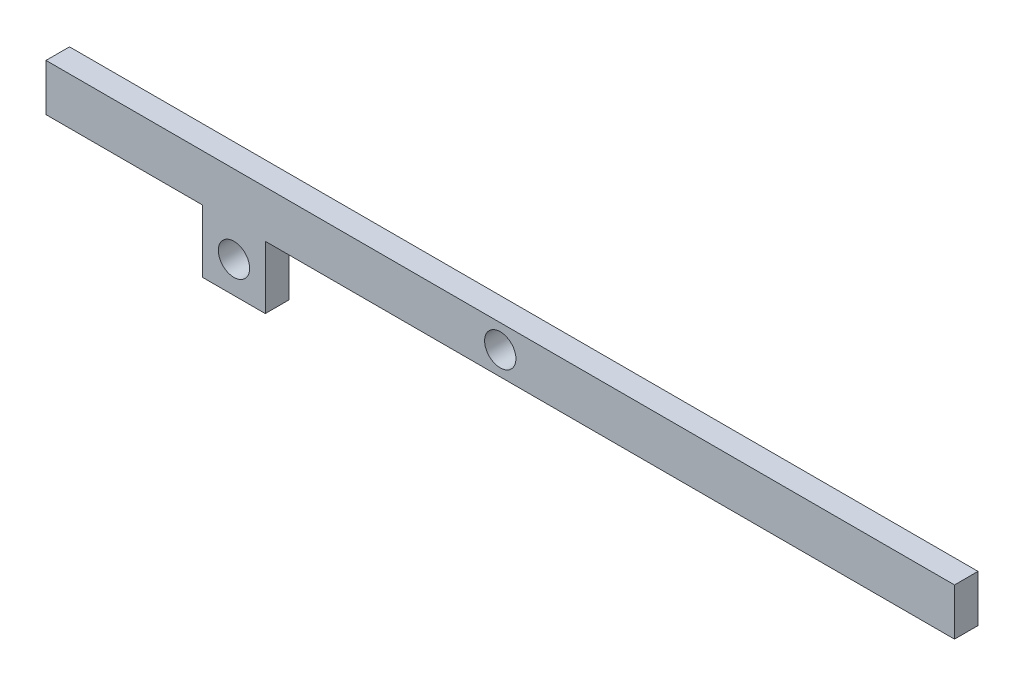
SolidWorks part; units mm, degrees
ref_plane "Front Plane" through (0, 0, 0) normal (0, 0, 1) x (1, 0, 0)
ref_plane "Top Plane" through (0, 0, 0) normal (0, 1, 0) x (1, 0, 0)
ref_plane "Right Plane" through (0, 0, 0) normal (1, 0, 0) x (0, 0, -1)
sketch "Sketch1" plane through (0, 0, 0) normal (0, 0, 1) x (1, 0, 0)
  line L1 (290, 15) -> (-290, 15)
  line L2 (290, 15) -> (290, -15)
  line L3 (290, -15) -> (-290, -15)
  line L4 (-290, 15) -> (-290, -15)
  line L5 (290, 15) -> (-290, -15) construction
  line L6 (290, -15) -> (-290, 15) construction
  point P0 (0, 0)
  dimension "D1" = 580
  dimension "D2" = 30
extrude "Boss-Extrude1" add sketch "Sketch1" along normal mid plane 15
sketch "Sketch2" plane through (0, 0, 7.5) normal (0, 0, 1) x (1, 0, 0)
  circle A0 centre (0, 0) radius 10
  dimension "D1" = 20
extrude "Cut-Extrude1" cut sketch "Sketch2" against normal blind 20
sketch "Sketch3" plane through (0, 0, 7.5) normal (0, 0, 1) x (1, 0, 0)
  line L0 (-290, -15) -> (290, -15) construction
  line L1 (-190, -15) -> (-150, -15)
  line L2 (-190, -15) -> (-190, -55)
  line L3 (-190, -55) -> (-150, -55)
  line L4 (-150, -15) -> (-150, -55)
  circle A0 centre (-170, -35) radius 10
  dimension "D4" = 20
  dimension "D1" = 40
  dimension "D2" = 40
  dimension "D3" = 100
  dimension "D5" = 20
  dimension "D6" = 20
extrude "Boss-Extrude2" add sketch "Sketch3" against normal blind 15
